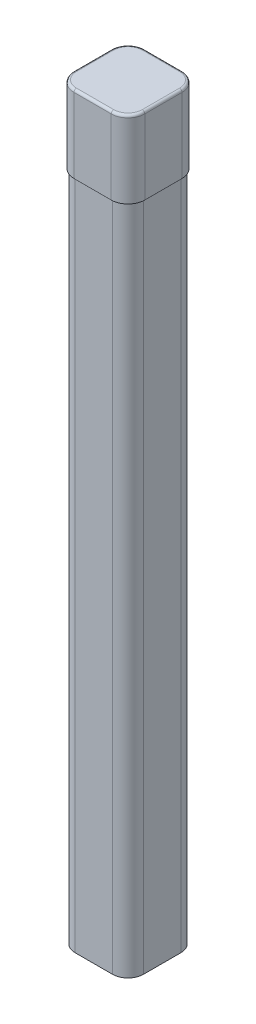
SolidWorks part; units mm, degrees
ref_plane "Front Plane" through (0, 0, 0) normal (0, 0, 1) x (1, 0, 0)
ref_plane "Top Plane" through (0, 0, 0) normal (0, 1, 0) x (1, 0, 0)
ref_plane "Right Plane" through (0, 0, 0) normal (1, 0, 0) x (0, 0, -1)
sketch "Sketch1" plane through (0, 0, 0) normal (0, 1, 0) x (1, 0, 0)
  line L0 (3.81, 6.731) -> (-3.81, 6.731)
  line L1 (3.81, -6.985) -> (-3.81, -6.985)
  line L2 (6.985, -3.81) -> (6.985, 3.81)
  line L3 (3.81, 6.985) -> (-3.81, 6.985)
  line L4 (-6.985, -3.81) -> (-6.985, 3.81)
  line L5 (6.985, -6.985) -> (-6.985, 6.985) construction
  line L6 (6.985, 6.985) -> (-6.985, -6.985) construction
  line L7 (-6.731, -3.81) -> (-6.731, 3.81)
  line L8 (3.81, -6.731) -> (-3.81, -6.731)
  line L9 (6.731, -3.81) -> (6.731, 3.81)
  arc A0 (-6.985, -3.81) -> (-3.81, -6.985) centre (-3.81, -3.81) ccw
  arc A1 (3.81, -6.985) -> (6.985, -3.81) centre (3.81, -3.81) ccw
  arc A2 (6.985, 3.81) -> (3.81, 6.985) centre (3.81, 3.81) ccw
  arc A3 (-3.81, 6.985) -> (-6.985, 3.81) centre (-3.81, 3.81) ccw
  arc A4 (-3.81, 6.731) -> (-6.731, 3.81) centre (-3.81, 3.81) ccw
  arc A5 (-6.731, -3.81) -> (-3.81, -6.731) centre (-3.81, -3.81) ccw
  arc A6 (3.81, -6.731) -> (6.731, -3.81) centre (3.81, -3.81) ccw
  arc A7 (6.731, 3.81) -> (3.81, 6.731) centre (3.81, 3.81) ccw
  point P0 (0, 0)
  dimension "D2" = 3.175
  dimension "D1" = 13.462
  dimension "D3" = 0.254
extrude "Boss-Extrude1" add sketch "Sketch1" along normal blind 152.4
sketch "Sketch2" plane through (0, 152.4, 0) normal (0, 1, 0) x (1, 0, 0)
  line L0 (-7.239, 3.81) -> (-7.239, -3.81)
  line L1 (-3.81, -7.239) -> (3.81, -7.239)
  line L2 (7.239, -3.81) -> (7.239, 3.81)
  line L3 (3.81, 7.239) -> (-3.81, 7.239)
  line L4 (-3.81, -6.985) -> (3.81, -6.985)
  line L5 (6.985, -3.81) -> (6.985, 3.81)
  line L6 (3.81, 6.985) -> (-3.81, 6.985)
  line L7 (-6.985, 3.81) -> (-6.985, -3.81)
  line L8 (-3.81, -6.985) -> (3.81, -6.985)
  line L9 (6.985, -3.81) -> (6.985, 3.81)
  line L10 (3.81, 6.985) -> (-3.81, 6.985)
  line L11 (-6.985, 3.81) -> (-6.985, -3.81)
  arc A0 (-3.81, 7.239) -> (-7.239, 3.81) centre (-3.81, 3.81) ccw
  arc A1 (-7.239, -3.81) -> (-3.81, -7.239) centre (-3.81, -3.81) ccw
  arc A2 (3.81, -7.239) -> (7.239, -3.81) centre (3.81, -3.81) ccw
  arc A3 (7.239, 3.81) -> (3.81, 7.239) centre (3.81, 3.81) ccw
  arc A4 (-6.985, -3.81) -> (-3.81, -6.985) centre (-3.81, -3.81) ccw
  arc A5 (3.81, -6.985) -> (6.985, -3.81) centre (3.81, -3.81) ccw
  arc A6 (6.985, 3.81) -> (3.81, 6.985) centre (3.81, 3.81) ccw
  arc A7 (-3.81, 6.985) -> (-6.985, 3.81) centre (-3.81, 3.81) ccw
  arc A8 (-6.985, -3.81) -> (-3.81, -6.985) centre (-3.81, -3.81) ccw
  arc A9 (3.81, -6.985) -> (6.985, -3.81) centre (3.81, -3.81) ccw
  arc A10 (6.985, 3.81) -> (3.81, 6.985) centre (3.81, 3.81) ccw
  arc A11 (-3.81, 6.985) -> (-6.985, 3.81) centre (-3.81, 3.81) ccw
  dimension "D1" = 0
  dimension "D2" = 0.254
extrude "Boss-Extrude2" add sketch "Sketch2" against normal blind 15.24 separate body contours L0 A1 L1 A2 L2 A3 L3 A0
sketch "Sketch3" plane through (0, 152.4, 0) normal (0, 1, 0) x (1, 0, 0)
  line L4 (-7.239, 3.81) -> (-7.239, -3.81)
  line L5 (-3.81, -7.239) -> (3.81, -7.239)
  line L6 (7.239, -3.81) -> (7.239, 3.81)
  line L7 (3.81, 7.239) -> (-3.81, 7.239)
  line L8 (-7.239, 3.81) -> (-7.239, -3.81)
  line L9 (-3.81, -7.239) -> (3.81, -7.239)
  line L10 (7.239, -3.81) -> (7.239, 3.81)
  line L11 (3.81, 7.239) -> (-3.81, 7.239)
  arc A4 (-3.81, 7.239) -> (-7.239, 3.81) centre (-3.81, 3.81) ccw
  arc A5 (-7.239, -3.81) -> (-3.81, -7.239) centre (-3.81, -3.81) ccw
  arc A6 (3.81, -7.239) -> (7.239, -3.81) centre (3.81, -3.81) ccw
  arc A7 (7.239, 3.81) -> (3.81, 7.239) centre (3.81, 3.81) ccw
  arc A8 (-3.81, 7.239) -> (-7.239, 3.81) centre (-3.81, 3.81) ccw
  arc A9 (-7.239, -3.81) -> (-3.81, -7.239) centre (-3.81, -3.81) ccw
  arc A10 (3.81, -7.239) -> (7.239, -3.81) centre (3.81, -3.81) ccw
  arc A11 (7.239, 3.81) -> (3.81, 7.239) centre (3.81, 3.81) ccw
  dimension "D1" = 0
extrude "Boss-Extrude3" add sketch "Sketch3" along normal blind 0.508
fillet "Fillet1" radius 0.508 8 edges at (-6.2347, 152.908, -6.2347) (0, 152.908, -7.239) (6.2347, 152.908, -6.2347) (7.239, 152.908, 0) (6.2347, 152.908, 6.2347) (0, 152.908, 7.239) (-6.2347, 152.908, 6.2347) (-7.239, 152.908, 0)
